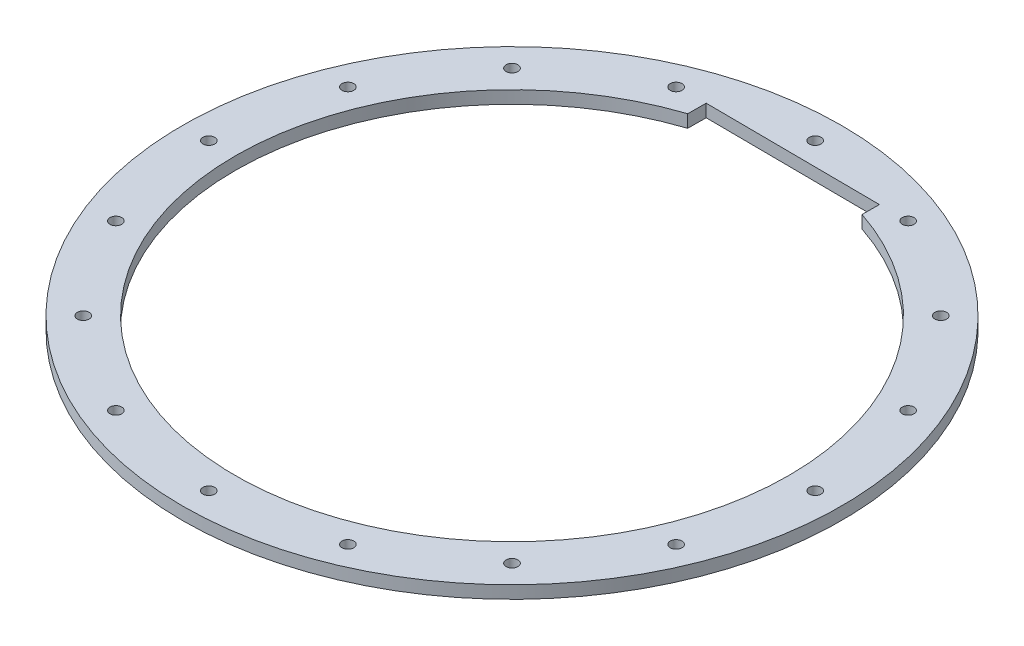
SolidWorks part; units mm, degrees
ref_plane "Front" through (0, 0, 0) normal (0, 0, 1) x (1, 0, 0)
ref_plane "Top" through (0, 0, 0) normal (0, 1, 0) x (1, 0, 0)
ref_plane "Right" through (0, 0, 0) normal (1, 0, 0) x (0, 0, -1)
sketch "Sketch2" plane through (0, 0, 0) normal (0, 1, 0) x (1, 0, 0)
  circle A0 centre (0, 0) radius 79.375
  circle A1 centre (0, 0) radius 73.025 construction
  circle A2 centre (0, 0) radius 66.675
  circle A3 centre (0, 73.025) radius 1.4224
  circle A4 centre (27.9455, 67.4663) radius 1.4224
  circle A5 centre (51.6365, 51.6365) radius 1.4224
  circle A6 centre (67.4663, 27.9455) radius 1.4224
  circle A7 centre (73.025, 0) radius 1.4224
  circle A8 centre (67.4663, -27.9455) radius 1.4224
  circle A9 centre (51.6365, -51.6365) radius 1.4224
  circle A10 centre (27.9455, -67.4663) radius 1.4224
  circle A11 centre (0, -73.025) radius 1.4224
  circle A12 centre (-27.9455, -67.4663) radius 1.4224
  circle A13 centre (-51.6365, -51.6365) radius 1.4224
  circle A14 centre (-67.4663, -27.9455) radius 1.4224
  circle A15 centre (-73.025, 0) radius 1.4224
  circle A16 centre (-67.4663, 27.9455) radius 1.4224
  circle A17 centre (-51.6365, 51.6365) radius 1.4224
  circle A18 centre (-27.9455, 67.4663) radius 1.4224
  point P40 (0, 0)
  dimension "D1" = 158.75
  dimension "D2" = 146.05
  dimension "D3" = 133.35
  dimension "D4" = 2.8448
  dimension "D5" = 16
extrude "Boss-Extrude1" add sketch "Sketch2" along normal blind 3.048
sketch "Sketch5" plane through (0, 0, 0) normal (0, -1, 0) x (-1, 0, 0)
  line L0 (0, 73.025) -> (-0.0635, 67.5688) construction
  line L1 (-21.0688, 67.4241) -> (20.9418, 67.7134) construction
  line L2 (20.9418, 67.7134) -> (-21.0688, 67.4241)
  line L3 (20.9418, 67.7134) -> (20.9722, 63.2908)
  line L4 (20.9418, 67.7134) -> (21.231, 25.7044) construction
  line L5 (-21.0688, 67.4241) -> (-21.0402, 63.2682)
  line L6 (-20.7796, 25.4151) -> (-21.0688, 67.4241) construction
  circle A0 centre (0, 0) radius 66.675 construction
  circle M13 centre (0, 0) radius 66.675
  dimension "D1" = 5.4562
extrude "Cut-Extrude2" cut sketch "Sketch5" against normal through all contours L2 L5 L3 M13
